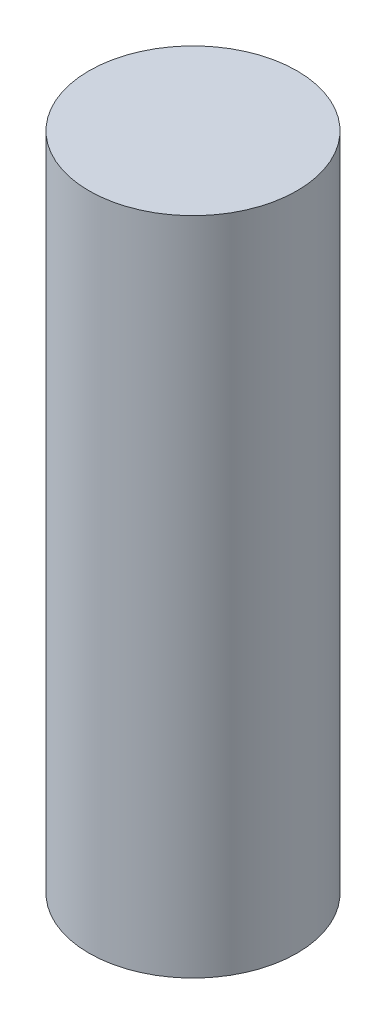
SolidWorks part; units mm, degrees
ref_plane "Front Plane" through (0, 0, 0) normal (0, 0, 1) x (1, 0, 0)
ref_plane "Top Plane" through (0, 0, 0) normal (0, 1, 0) x (1, 0, 0)
ref_plane "Right Plane" through (0, 0, 0) normal (1, 0, 0) x (0, 0, -1)
sketch "Sketch1" plane through (0, 0, 0) normal (0, 1, 0) x (1, 0, 0)
  circle A0 centre (0, 0) radius 2
  dimension "D1" = 4
extrude "Boss-Extrude1" add sketch "Sketch1" along normal blind 12.7
